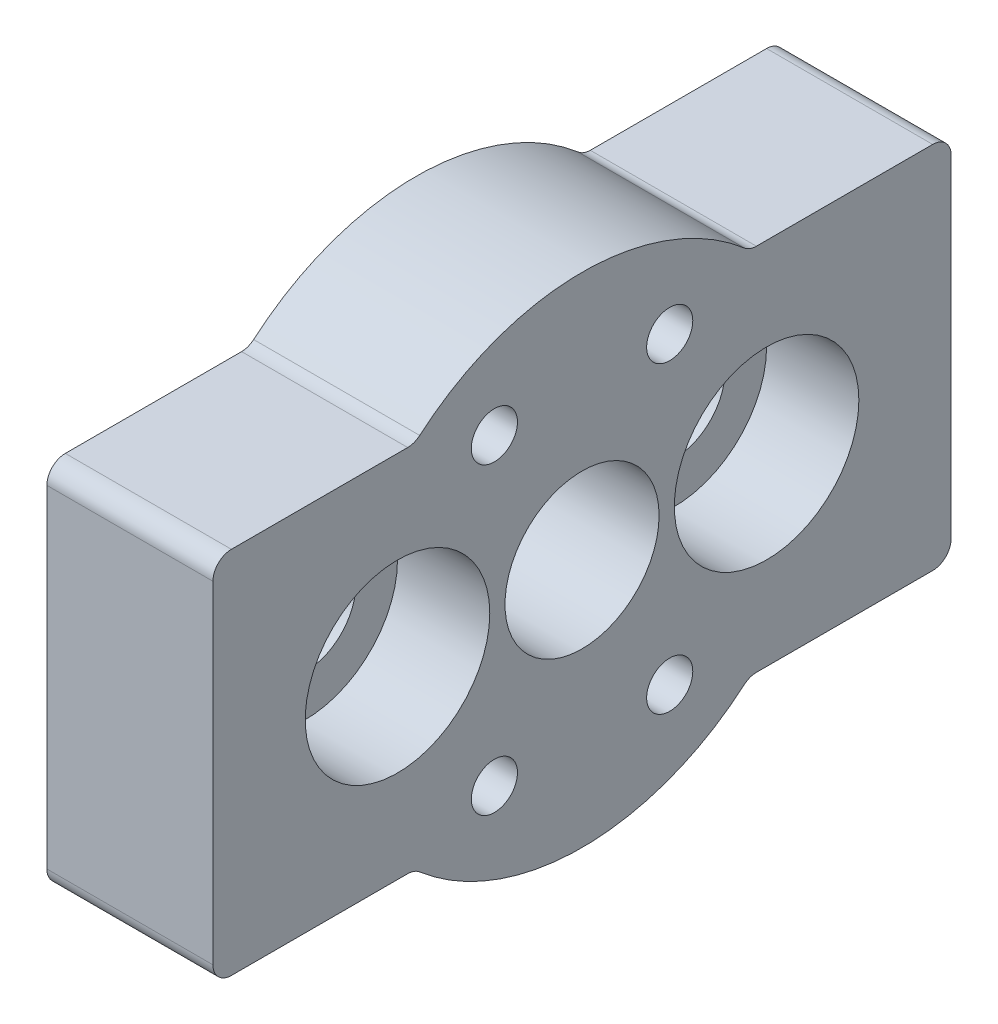
SolidWorks part; units mm, degrees
material "ABS"
ref_plane "Front Plane" through (0, 0, 0) normal (0, 0, 1) x (1, 0, 0)
ref_plane "Top Plane" through (0, 0, 0) normal (0, 1, 0) x (1, 0, 0)
ref_plane "Right Plane" through (0, 0, 0) normal (1, 0, 0) x (0, 0, -1)
sketch "Rotary Plate Sketch" plane through (0, 0, 0) normal (1, 0, 0) x (0, 0, -1)
  line L1 (-20, -10) -> (20, -10)
  line L2 (-20, -10) -> (-20, 10)
  line L3 (-20, 10) -> (20, 10)
  line L4 (20, -10) -> (20, 10)
  line L5 (0, 10) -> (0, -10) construction
  line L6 (-20, 0) -> (20, 0) construction
  line L7 (-20, 10) -> (0, -10) construction
  line L8 (0, -10) -> (20, 10) construction
  line L9 (0, 0) -> (4.75, 8.2272) construction
  circle A2 centre (-10, 0) radius 5 construction
  circle A3 centre (10, 0) radius 5 construction
  circle A4 centre (0, 0) radius 9.5 construction
  circle A5 centre (4.75, 8.2272) radius 1.5 construction
  circle A6 centre (0, 0) radius 4.175
  arc A10 (-9.0692, -10) -> (9.0692, -10) centre (0, 0) ccw
  arc A11 (-9.0692, 10) -> (9.0692, 10) centre (0, 0) cw
  point P0 (0, 0)
  point P6 (10, 0)
  point P7 (-10, 0)
  point P8 (4.75, 8.2272)
  dimension "Countersink Diameter" = 10
  dimension "D5" = 3
  dimension "LeadScrewDiameter" = 8.35
  dimension "ExcessFlangeR" = 13.5
  dimension "D1" = 40
  dimension "BoltCircleRadiud" = 9.5
  dimension "LeadScrewHeight" = 10
  dimension "D6" = 30
  dimension "D2" = 20
extrude "Y Plate Boss-Extrude" add sketch "Rotary Plate Sketch" against normal blind 9 contours A11 L3 | L1 L4 L3 L2 A6 | L1 A10
hole_wizard "CBORE for M5 SHCS1" positions "Sketch4" profile "Sketch5" counterbore size "M5" standard "ANSI Metric" end condition through all
sketch "Sketch4" plane through (0, 0, 0) normal (1, 0, 0) x (0, 0, -1)
  point P0 (-10, 0)
  point P3 (10, 0)
sketch "Sketch5" plane through (0, 0, 10) normal (0, 1, 0) x (0, 0, -1)
  line L0 (0, 0) -> (0, 9)
  line L1 (0, 9) -> (2.75, 9)
  line L3 (2.75, 9) -> (2.75, 5)
  line L4 (2.75, 5) -> (5, 5)
  line L5 (5, 5) -> (5, 0)
  line L7 (5, 0) -> (0, 0)
  line L11 (0, -6.35) -> (0, 107.95) construction
  dimension "Thru Hole Dia." = 5.5
  dimension "Thru Hole Depth" = 9
  dimension "C'Bore Dia." = 10
  dimension "C'Bore Depth" = 5
fillet "Fillet1" radius 1 8 edges at (-4.5, -10, 20) (-4.5, -10, 9.0692) (-4.5, -10, -9.0692) (-4.5, -10, -20) (-4.5, 10, -20) (-4.5, 10, -9.0692) (-4.5, 10, 9.0692) (-4.5, 10, 20)
hole_wizard "Tap Drill for M3x0.5 Tap1" positions "Sketch6" profile "Sketch7" hole size "M3x0.5" standard "ANSI Metric" end condition through all
sketch "Sketch6" plane through (0, 0, 0) normal (1, 0, 0) x (0, 0, -1)
  point P0 (4.75, 8.2272)
sketch "Sketch7" plane through (0, 8.2272, -4.75) normal (0, 1, 0) x (0, 0, -1)
  line L0 (0, 0) -> (0, 9)
  line L1 (0, 9) -> (1.25, 9)
  line L2 (1.25, 9) -> (1.25, 0)
  line L5 (1.25, 0) -> (0, 0)
  line L11 (0, -6.35) -> (0, 107.95) construction
  dimension "Thru Hole Dia." = 2.5
  dimension "Thru Hole Depth" = 9
pattern_circular "CirPattern1" count 6 every 60 about axis through (-9, 0, 0) along (1, 0, 0) skipping 1, 4 of "Tap Drill for M3x0.5 Tap1"
equation "\"ExtrusionStandard\"= 20mm'Size of extrusion used for framing"
equation "\"BaseExtrusionFrameWidth\"= 60mm'Width of the central aluminum extrusion"
equation "\"BaseExtrusionFrameHeight\"= 20mm'Height of the central aluminum extrusion"
equation "\"PlateThickness\"= 15mm'Thickness of the the front and back framing plates"
equation "\"RailHeight\"= 13mm'Total height of the carriage and rail component"
equation "\"WallThickness\"= 3mm'Standard wall thickness"
equation "\"ShaftDiameter\"= 20mm'Outside Diameter of the main yoke shaft"
equation "\"ShaftClearance\"= 1mm'Clearance/gap between the main yoke and non-bearing elements"
equation "\"PlainBearingBoltCircleDiameter\"= ( \"WallThickness\" + \"M3_ClearanceDiameter\" / 2 ) * 2 + \"PlainBearingOD\"'Bolt circle diameter for the plain bearing retainer/mount"
equation "\"PlainBearingBoltcount\"= 5'Number of bolts used in the plain bearing/mount"
equation "\"D1@Rotary Plate Sketch\" = \"ExtrusionStandard\" * 2"
equation "\"LeadScrewDiameter\"= 6.35mm'OD of the leadsrew used on the Y axis"
equation "\"LeadScrewDiameter@Rotary Plate Sketch\"=\"LeadScrewDiameter\"+\"ShaftClearance\"*2"
equation "\"LeadScrewHeight\"= 10mm'Height of the center of the Lead screw from bottom of gantry extrusion"
equation "\"LeadScrewHeight@Rotary Plate Sketch\"=\"LeadScrewHeight\""
equation "\"D2@Rotary Plate Sketch\"=\"ExtrusionStandard\""
equation "\"LeadScrewNut_FlangeOD\"= 25mm'OD of the lead screw nut flange"
equation "\"LeadScrewNut_BoltCircleDiameter\"= 19mm'Bolt circle diameter needed to mount the leadscrew nut"
equation "\"LeadScrewNut_BoltCount\"= 6'Number of bolts required to mount the leadscrew nut to gantry."
equation "\"ExcessFlangeR@Rotary Plate Sketch\"=(\"LeadScrewNut_FlangeOD\" / 2)+1mm"
equation "\"BoltCircleRadiud@Rotary Plate Sketch\"=\"LeadScrewNut_BoltCircleDiameter\"/2"
equation "\"X_ThrustBearingOD\"= 35mm'OD of the thrust bearing used on the main shaft"
equation "\"X_ThrustBearingID\"= 20mm'ID of the thrust bearing used on the main shaft"
equation "\"X_ThrustBearingThickness\"= 10mm'Thickness of the thrust bearing used on the main shaft"
equation "\"X_RearCollarOD\"= 32mm'OD of the shaft collar of the main shaft"
equation "\"X_RearCollarID\"= 20mm'ID of the shaft collar of the main shaft"
equation "\"X_RearCollarThickness\"= 14mm'Thickness of the collar along the main shaft"
equation "\"ShaftOffset_BaseThickness\"= 6mm + \"WallThickness\"'FIXME"
equation "\"PillowHeight\"= \"ShaftOffset_BaseThickness\" + \"ExtrusionStandard\"'Height of the main shaft, as measured from the top of the gantry surface"
equation "\"X_BeltPitch\"= 2mm'Pitch of the timing belt used on the X axis/main shaft."
equation "\"X_Drive_Teeth\"= 20'Number of teeth used on the X/Main stepper motor pulley"
equation "\"X_Shaft_Teeth\"= 60'Number of teeth on the X/Main shaft pulley"
equation "\"X_Drive_PD\"= ( \"X_Drive_Teeth\" * \"X_BeltPitch\" ) / PI'Pitch Diameter of the X/main motor pulley"
equation "\"X_Shaft_PD\"= ( \"X_Shaft_Teeth\" * \"X_BeltPitch\" ) / PI'Pitch Diameter of the X/main shaft pulley"
equation "\"X_CenterDistance\"= 55mm'Distance between the main shaft and motor pulley centers"
equation "\"GantryLength\"= 150mm'Length of the gantry extrusion/plate"
equation "\"X_MotorPlateThickness\"= 15mm'Thickness of the plate used to hold the X/main motor"
equation "\"X_MotorPlateLength\"= \"X_MotorPlateThickness\" + \"ExtrusionStandard\" * 2'FIXME"
equation "\"X_BeltWidth\"= 10mm'Width of the timing belt used on the X/Main shaft rotary drive"
equation "\"X_PillowLength\"= ( \"WallThickness\" * 4 ) + \"X_RearCollarThickness\" + ( \"X_ThrustBearingThickness\" * 2 ) + \"X_ShaftRotaryBearingThickness\"'Total length of the pillow block used to hold the main shaft"
equation "\"X_ShaftRotaryBearingThickness\"= 9mm'Thickness of the radial bearing used on the main shaft"
equation "\"X_ShaftRotaryBearingOD\"= 37mm'OD of the radial bearing used on the main shaft"
equation "\"ShaftLength\"= 400mm'Length of the main shaft."
equation "\"PlainBearingOD\"= 31.8mm'OD of the Plain Bearing housing"
equation "\"Y_Drive_Length\"= \"ShaftLength\"'duplicate"
equation "\"Y_Drive_Diameter\"= \"LeadScrewDiameter\"'duplicate"
equation "\"Y_Drive_ThrustBearingOD\"= .5625in'OD of the thrust bearings used to support the leadscrew/Y drive"
equation "\"Y_Drive_ThrustBearingThickness\"= .193in'Thickness of the thrust bearings used to support the leadscrew/Y drive"
equation "\"Y_Drive_ShaftCollarOD\"= .6875in'OD of the collar used to constrain the leadscrew/Y drive"
equation "\"Y_Drive_ShaftCollarThickness\"= .3125in'Thickness of the collar used to constrain the leadscrew/Y drive"
equation "\"Y_Drive_ShaftCollarClearance\"= .375in / 2'Amount of radial clearance needed around the leadscrew/Y shaft collar"
equation "\"calc_Y_Drive_BearingLargestDiameter\"= IIF ( \"Y_Drive_ThrustBearingOD\" > \"Y_Drive_ShaftCollarOD\" , \"Y_Drive_ThrustBearingOD\" , \"Y_Drive_ShaftCollarOD\" )'FIXME - calculated diameter needed for Y drive pillow - needs to account for collar clearance."
equation "\"Y_Drive_BearingBoltCircleDiameter\"= \"calc_Y_Drive_BearingLargestDiameter\" + ( \"Y_Drive_ShaftCollarClearance\" * 2 ) + ( \"WallThickness\" * 2 ) + 2 * 10mm'FIXME - unused?"
equation "\"M3_ClearanceDiameter\"= 8mm'Keepout diameter for M3 holes"
equation "\"M5_ClearanceDiameter\"= 10mm'Keepout Diameter for M5 holes"
equation "\"Y_Drive_CenterDistance\"= 65mm'Center Distance between Y motor drive and leadscrew pulley"
equation "\"Y_Drive_Teeth\"= 20'Number of teeth on the Y/linear stepper pulley"
equation "\"Y_Drive_ShaftTeeth\"= 60'Number of teeth on the Y/linear leadscrew pulley"
equation "\"Y_Drive_BeltWidth\"= 10mm'Width of the belt used on the Y/linear drive"
equation "\"Y_Drive_BeltPitch\"= 2mm'Pitch of the timing belt used on the Y/linear drive"
equation "\"Y_Drive_PD\"= ( \"Y_Drive_Teeth\" * \"Y_Drive_BeltPitch\" ) / PI'Pitch Diameter of the stepper pulley for the Y/linear drive"
equation "\"Y_Drive_ShaftPD\"= ( \"Y_Drive_ShaftTeeth\" * \"Y_Drive_BeltPitch\" ) / PI'Pitch diameter of the pulley on the Y/linear leadscrew"
equation "\"PlainBearingLength\"= 44.8mm'Length of the plain bearing housing"
equation "\"Y_Drive_ShaftBearingThickness\"= .1875in'Thickness of the radial bearing used to support the Y leadscrew"
equation "\"Y_Drive_ShaftBearingOD\"= .625in'OD of the radial bearing used to support the Y leadscrew"
equation "\"EncoderMount_BoltWidth\"= 80mm"
equation "\"EncoderMount_BoltRowCount\" = 1"
equation "\"EncoderMount_BoltRowDistance\"= 20mm"
equation "\"EncoderMount_Offset\"= 10mm"
equation "\"Y_Drive_StepperShaftLength\"= 21mm"
equation "\"X_StepperShaftLength\" = 21mm"
equation "\"Y_DriveStepperShaftDiameter\"= 6.35mm"
equation "\"X_StepperShaftDiameter\"= 6.35mm"
